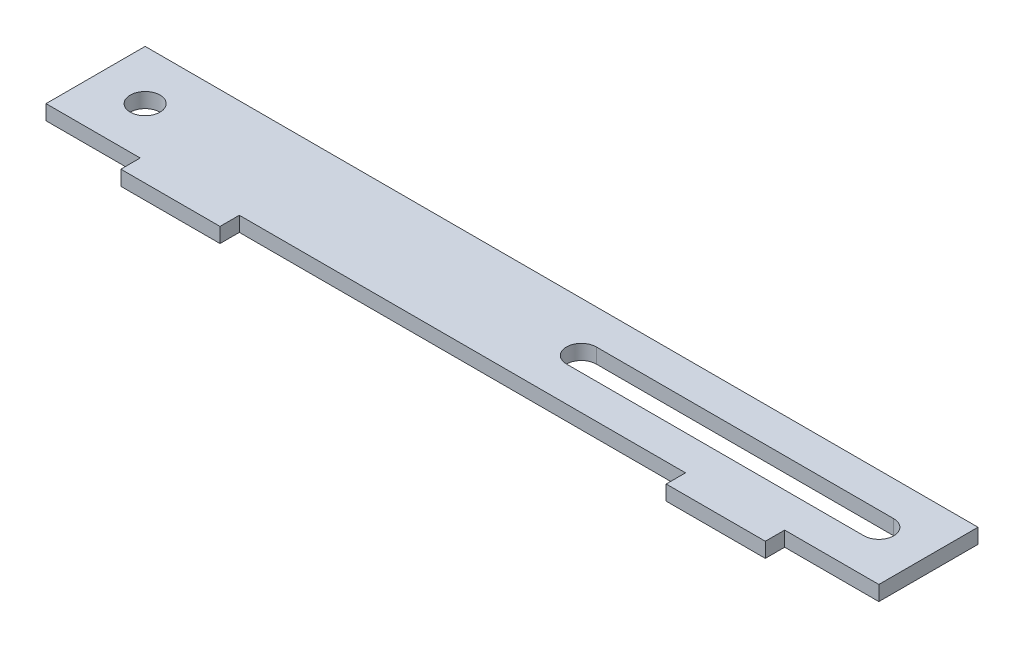
SolidWorks part; units mm, degrees
material "Acrylic (Medium-high impact)"
ref_plane "Front Plane" through (0, 0, 0) normal (0, 0, 1) x (1, 0, 0)
ref_plane "Top Plane" through (0, 0, 0) normal (0, 1, 0) x (1, 0, 0)
ref_plane "Right Plane" through (0, 0, 0) normal (1, 0, 0) x (0, 0, -1)
sketch "Sketch1" plane through (0, 0, 0) normal (0, 1, 0) x (1, 0, 0)
  line L0 (158, 10) -> (98, 10) construction
  line L1 (0, 0) -> (19, 0)
  line L2 (0, 0) -> (0, 20)
  line L3 (0, 20) -> (168, 20)
  line L4 (168, 0) -> (168, 20)
  line L5 (158, 7) -> (98, 7)
  line L6 (158, 13) -> (98, 13)
  line L7 (84, 20) -> (84, 0) construction
  line L9 (19, 0) -> (19, -3.9)
  line L10 (19, -3.9) -> (39, -3.9)
  line L11 (39, 0) -> (39, -3.9)
  line L12 (149, -3.9) -> (129, -3.9)
  line L13 (129, 0) -> (129, -3.9)
  line L15 (149, 0) -> (149, -3.9)
  line L16 (39, 0) -> (129, 0)
  line L17 (149, 0) -> (168, 0)
  circle A1 centre (10, 10) radius 3
  arc A2 (158, 7) -> (158, 13) centre (158, 10) ccw
  arc A3 (98, 13) -> (98, 7) centre (98, 10) ccw
  point P9 (128, 10)
  dimension "D3" = 6
  dimension "D7" = 3
  dimension "D1" = 168
  dimension "D2" = 20
  dimension "D4" = 10
  dimension "D5" = 10
  dimension "D6" = 10
  dimension "D8" = 60
  dimension "D9" = 3.9
  dimension "D10" = 20
  dimension "D11" = 45
extrude "Boss-Extrude1" add sketch "Sketch1" along normal blind 3
